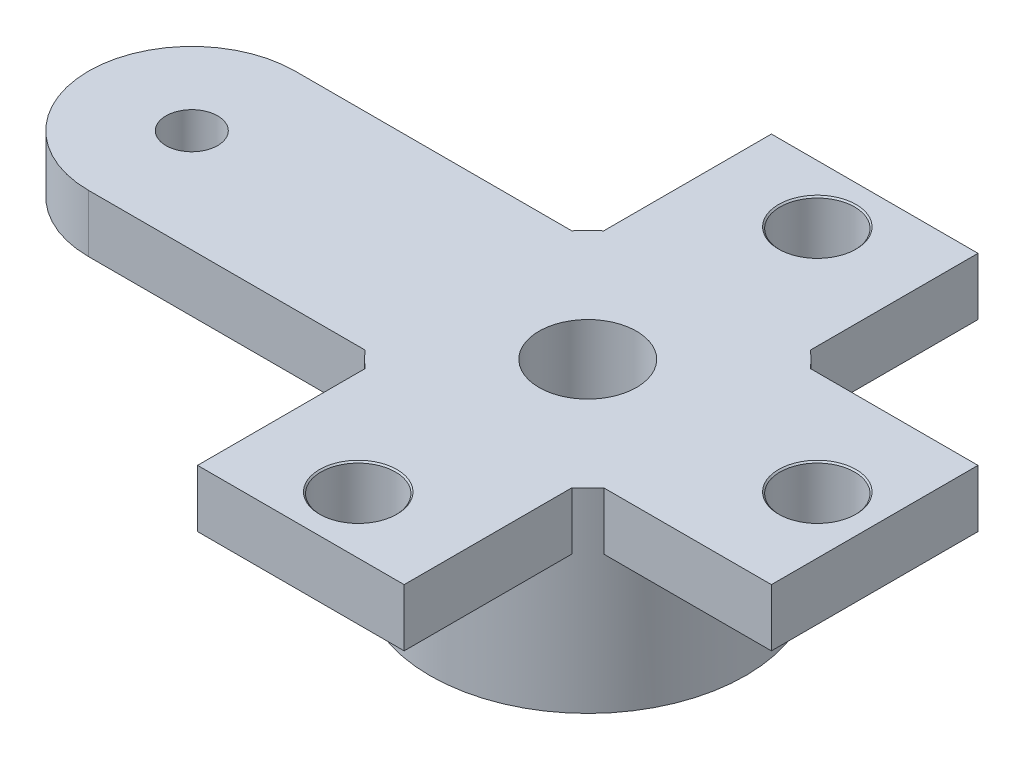
SolidWorks part; units mm, degrees
ref_plane "Спереди" through (0, 0, 0) normal (0, 0, 1) x (1, 0, 0)
ref_plane "Сверху" through (0, 0, 0) normal (0, 1, 0) x (1, 0, 0)
ref_plane "Справа" through (0, 0, 0) normal (1, 0, 0) x (0, 0, -1)
sketch "Эскиз1" plane through (0, 0, 0) normal (0, 1, 0) x (1, 0, 0)
  circle A0 centre (0, 0) radius 2.75
  circle A1 centre (0, 0) radius 0.85
  dimension "D1" = 5.5
  dimension "D2" = 1.7
extrude "Бобышка-Вытянуть1" add sketch "Эскиз1" along normal blind 3.4
sketch "Эскиз2" plane through (0, 3.4, 0) normal (0, 1, 0) x (1, 0, 0)
  line L0 (2.0791, 1.8) -> (6.9, 1.8)
  line L1 (2.0791, -1.8) -> (6.9, -1.8)
  line L2 (-1.8, -2.0791) -> (-1.8, -6.9)
  line L3 (1.8, -2.0791) -> (1.8, -6.9)
  line L4 (-2.0791, 1.8) -> (-6.9, 1.8)
  line L5 (-2.0791, -1.8) -> (-6.9, -1.8)
  line L6 (1.8, 2.0791) -> (1.8, 6.9)
  line L7 (-1.8, 2.0791) -> (-1.8, 6.9)
  circle A0 centre (0, 0) radius 2.75 construction
  arc A1 (6.9, -1.8) -> (6.9, 1.8) centre (6.9, 0) ccw
  arc A2 (-1.8, -6.9) -> (1.8, -6.9) centre (0, -6.9) ccw
  arc A3 (-6.9, 1.8) -> (-6.9, -1.8) centre (-6.9, 0) ccw
  arc A4 (1.8, 6.9) -> (-1.8, 6.9) centre (0, 6.9) ccw
  circle A5 centre (0, 0) radius 2.75
  circle A9 centre (-6.9, 0) radius 0.45
  circle A10 centre (0, 6.9) radius 0.45
  circle A11 centre (6.9, 0) radius 0.45
  circle A12 centre (0, -6.9) radius 0.45
  circle M1 centre (0, 0) radius 2.75
  dimension "D2" = 6.9
  dimension "D4" = 0.9
  dimension "D1" = 3.6
  dimension "D3" = 4
extrude "Бобышка-Вытянуть2" add sketch "Эскиз2" against normal blind 1 contours L4 A3 L5 M1 | L6 A4 L7 M1 | L1 A1 L0 M1 | L2 A2 L3 M1
sketch "Эскиз3" plane through (0, 3.4, 0) normal (0, 1, 0) x (1, 0, 0)
  line L0 (-1.8, 5) -> (1.8, 5)
  line L1 (-1.8, 2.0791) -> (-1.8, 6.9) construction
  line L2 (1.8, 2.0791) -> (1.8, 6.9) construction
  line L3 (1.8, 5) -> (5, 1.8)
  line L4 (2.0791, 1.8) -> (6.9, 1.8) construction
  line L5 (5, 1.8) -> (5, -1.8)
  line L6 (2.0791, -1.8) -> (6.9, -1.8) construction
  line L7 (5, -1.8) -> (1.8, -5)
  line L8 (1.8, -2.0791) -> (1.8, -6.9) construction
  line L9 (1.8, -5) -> (-1.8, -5)
  line L10 (-1.8, -2.0791) -> (-1.8, -6.9) construction
  line L11 (-2.0791, 1.8) -> (-6.9, 1.8) construction
  line L12 (-2.0791, -1.8) -> (-6.9, -1.8) construction
  line L13 (-1.8, 5) -> (-7.7949, 1.8)
  line L14 (-7.7949, -1.8) -> (-1.8, -5)
  circle A0 centre (0, 0) radius 0.85 construction
  arc A1 (-7.7949, 1.8) -> (-7.7949, -1.8) centre (0, 0) ccw
  circle A2 centre (0, 0) radius 2.75 construction
  line M2 (-1.8, -2.0791) -> (-1.8, -6.9)
  arc M3 (-1.8, -6.9) -> (1.8, -6.9) centre (0, -6.9) ccw
  line M4 (1.8, -6.9) -> (1.8, -2.0791)
  line M6 (2.0791, -1.8) -> (6.9, -1.8)
  arc M7 (6.9, -1.8) -> (6.9, 1.8) centre (6.9, 0) ccw
  line M8 (6.9, 1.8) -> (2.0791, 1.8)
  line M10 (1.8, 2.0791) -> (1.8, 6.9)
  arc M11 (1.8, 6.9) -> (-1.8, 6.9) centre (0, 6.9) ccw
  line M12 (-1.8, 6.9) -> (-1.8, 2.0791)
  circle M19 centre (0, 6.9) radius 0.45
  circle M20 centre (6.9, 0) radius 0.45
  circle M21 centre (0, -6.9) radius 0.45
  dimension "D2" = 5
  dimension "D3" = 8
  dimension "D1" = 5
extrude "Вырез-Вытянуть1" cut sketch "Эскиз3" against normal through all contours L5 M8 M6 M7 M20 | L9 M4 M2 M3 M21 | L0 M12 M10 M11 M19
hole_wizard "Диаметр отверстия Ø1.3 (1.3)1" positions "Эскиз5" profile "Эскиз4" hole size "Ø1.3" standard "Ansi (метрические)" end condition up to next
sketch "Эскиз5" plane through (0, 2.4, 0) normal (0, -1, 0) x (1, 0, 0)
  circle A0 centre (0, 0) radius 0.85 construction
  point P0 (0, -4)
  point P1 (4, 0)
  point P3 (0, 4)
  dimension "D1" = 4
  dimension "D2" = 4
  dimension "D3" = 4
sketch "Эскиз4" plane through (0, 2.4, -4) normal (1, 0, 0) x (0, 0, -1)
  line L0 (0, 0) -> (0, 1)
  line L1 (0, 1) -> (0.675, 1)
  line L2 (0.65, 0.975) -> (0.65, 0.025)
  line L3 (0.65, 0.025) -> (0.675, 0)
  line L5 (0.675, 0) -> (0, 0)
  line L6 (-0.65, 0.025) -> (-0.675, 0) construction
  line L7 (0.675, 1) -> (0.65, 0.975)
  line L8 (-0.675, 1) -> (-0.65, 0.975) construction
  line L11 (0, -6.35) -> (0, 107.95) construction
  dimension "Диаметр сквозного отверстия" = 1.3
  dimension "Глубина сквозного отверстия" = 1
  dimension "Диаметр передней зенковки" = 1.35
  dimension "Угол передней зенковки" = 90
  dimension "Диаметр задней зенковки" = 1.35
  dimension "Угол задней зенковки" = 90
